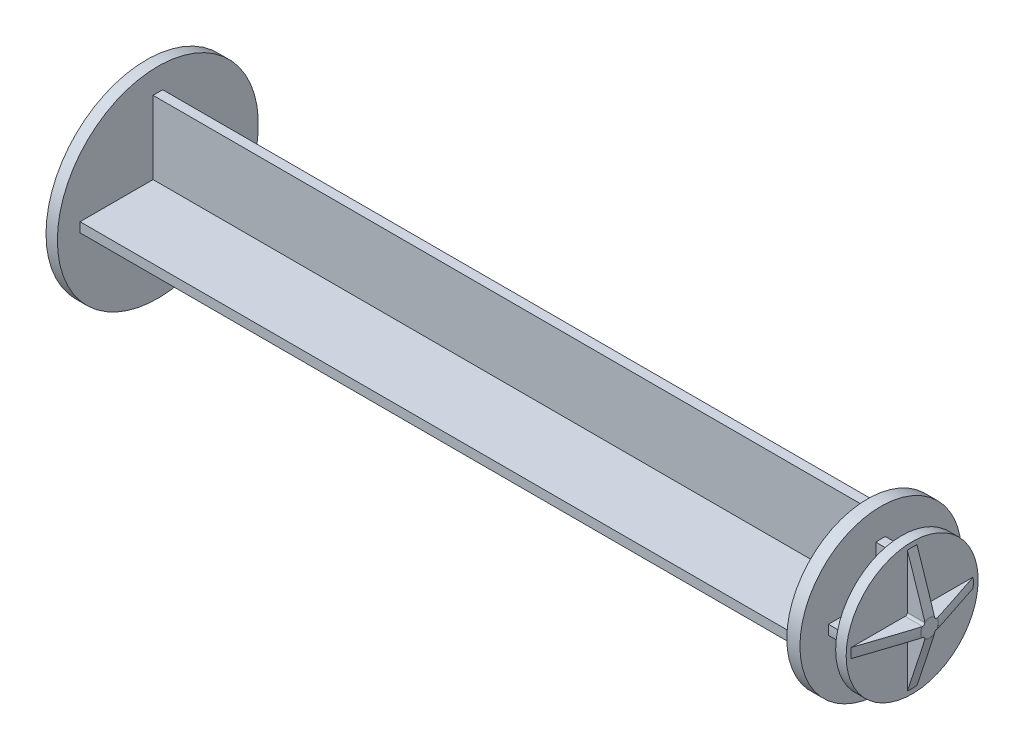
SolidWorks part; units mm, degrees
ref_plane "Front Plane" through (0, 0, 0) normal (0, 0, 1) x (1, 0, 0)
ref_plane "Top Plane" through (0, 0, 0) normal (0, 1, 0) x (1, 0, 0)
ref_plane "Right Plane" through (0, 0, 0) normal (1, 0, 0) x (0, 0, -1)
sketch "Sketch1" plane through (0, 0, 0) normal (0, 0, 1) x (1, 0, 0)
  line L0 (-3.3056, 0) -> (125.6458, 0) construction
  line L1 (16.4016, 0) -> (-16.4016, 0) construction
  line L2 (0, 0) -> (0, 14.605)
  line L3 (0, 14.605) -> (1.651, 14.605)
  line L4 (1.651, 14.605) -> (1.651, 11.7348)
  line L5 (1.651, 11.7348) -> (106.68, 11.7348)
  line L7 (111.252, 8.89) -> (113.7757, 1.3189)
  line L8 (113.792, 1.2185) -> (113.792, 0)
  line L9 (113.792, 0) -> (0, 0)
  line L10 (0, -16.3918) -> (0, 16.3918) construction
  line L12 (106.68, 11.7348) -> (106.68, 9.5885)
  line L13 (106.68, 9.5885) -> (111.252, 9.5885)
  line L14 (111.252, 9.5885) -> (111.252, 8.89)
  arc A0 (113.7757, 1.3189) -> (113.792, 1.2185) centre (113.4745, 1.2185) cw
  point P15 (113.792, 1.27)
  dimension "D10" = 0.3175
  dimension "D1" = 1.651
  dimension "D2" = 29.21
  dimension "D3" = 23.4696
  dimension "D4" = 106.68
  dimension "D5" = 17.78
  dimension "D6" = 19.177
  dimension "D7" = 2.54
  dimension "D8" = 111.252
  dimension "D9" = 2.54
revolve "Revolve: Main Body" add sketch "Sketch1" angle 360 about L0
sketch "Sketch2" plane through (1.651, 0, 0) normal (1, 0, 0) x (0, 0, -1)
  line L0 (0, 7.732) -> (0, -7.732) construction
  line L1 (-0.6985, 11.303) -> (0.6985, 11.303)
  line L2 (-0.6985, 11.303) -> (-0.6985, 0.6985)
  line L3 (-0.6985, -11.303) -> (0.6985, -11.303)
  line L4 (0.6985, 11.303) -> (0.6985, 0.6985)
  line L5 (-11.303, 0.6985) -> (-0.6985, 0.6985)
  line L6 (-11.303, 0.6985) -> (-11.303, -0.6985)
  line L7 (-11.303, -0.6985) -> (-0.6985, -0.6985)
  line L8 (11.303, 0.6985) -> (11.303, -0.6985)
  line L9 (-7.732, 0) -> (7.732, 0) construction
  line L10 (16.4016, 0) -> (-16.4016, 0) construction
  line L11 (0, 18.1835) -> (0, -18.1835) construction
  line L12 (0.6985, 0.6985) -> (11.303, 0.6985)
  line L13 (-0.6985, -0.6985) -> (-0.6985, -11.303)
  line L14 (0.6985, -0.6985) -> (11.303, -0.6985)
  line L15 (0.6985, -0.6985) -> (0.6985, -11.303)
  dimension "D1" = 1.397
  dimension "D2" = 1.397
  dimension "D3" = 22.606
  dimension "D4" = 22.606
extrude "Cut-Extrude: Pusher Side Cross" cut sketch "Sketch2" along normal offset from surface (103.124 mm away) 1.905 flip side to cut up to face at (106.68, 0, 11.7348)
sketch "Sketch3" plane through (106.68, 0, 0) normal (1, 0, 0) x (0, 0, -1)
  line L0 (-11.303, 0.6985) -> (-0.6985, 0.6985) construction
  line L1 (-11.303, -0.6985) -> (-0.6985, -0.6985) construction
  line L2 (-0.6985, -0.6985) -> (-0.6985, -11.303) construction
  line L3 (0.6985, -0.6985) -> (0.6985, -11.303) construction
  line L4 (0.6985, -0.6985) -> (11.303, -0.6985) construction
  line L5 (0.6985, 0.6985) -> (11.303, 0.6985) construction
  line L6 (0.6985, 11.303) -> (0.6985, 0.6985) construction
  line L7 (-0.6985, 11.303) -> (-0.6985, 0.6985) construction
  line L8 (-11.714, 0.6985) -> (-0.6985, 0.6985)
  line L9 (-11.714, -0.6985) -> (-0.6985, -0.6985)
  line L10 (-0.6985, -0.6985) -> (-0.6985, -11.714)
  line L11 (0.6985, -0.6985) -> (0.6985, -11.714)
  line L12 (0.6985, -0.6985) -> (11.714, -0.6985)
  line L13 (0.6985, 0.6985) -> (11.714, 0.6985)
  line L14 (0.6985, 11.714) -> (0.6985, 0.6985)
  line L15 (-0.6985, 11.714) -> (-0.6985, 0.6985)
  line L20 (-7.8512, 0) -> (7.8512, 0) construction
  line L21 (0, 7.8512) -> (0, -7.8512) construction
  line L22 (0, 18.1835) -> (0, -18.1835) construction
  line L23 (16.4016, 0) -> (-16.4016, 0) construction
  arc A1 (-0.6985, 11.714) -> (-11.714, 0.6985) centre (0, 0) ccw
  arc A2 (-11.714, -0.6985) -> (-0.6985, -11.714) centre (0, 0) ccw
  arc A3 (0.6985, -11.714) -> (11.714, -0.6985) centre (0, 0) ccw
  arc A4 (11.714, 0.6985) -> (0.6985, 11.714) centre (0, 0) ccw
  circle A5 centre (0, 0) radius 11.7348 construction
  arc A6 (-7.5879, 0.6985) -> (-7.5879, -0.6985) centre (0, 0) ccw
  arc A7 (7.5879, -0.6985) -> (7.5879, 0.6985) centre (0, 0) ccw
  arc A8 (0.6985, 7.5879) -> (-0.6985, 7.5879) centre (0, 0) ccw
  arc A9 (-0.6985, -7.5879) -> (0.6985, -7.5879) centre (0, 0) ccw
  circle M18 centre (0, 0) radius 11.7348
  circle M19 centre (0, 0) radius 9.5885
  dimension "D1" = 15.24
extrude "Cut-Extrude: Cross 2" cut sketch "Sketch3" along normal blind 3.048 contours L15 L8 M18 M19 | L14 L13 M18 M19 | L12 L11 M19 M18 | L10 L9 M19 M18 | L15 L8 M19 | L14 L13 M19 | L12 L11 M19 | L10 L9 M19 | A9 L10 L11 M19 | A8 L14 L15 M19 | L15 L14 M18 M19 | L11 L10 M19 M18 | L13 L12 M19 M18 | A7 L12 L13 M19 | A6 L8 L9 M19 | L9 L8 M18 M19
sketch "Sketch8" plane through (111.252, 0, 0) normal (1, 0, 0) x (0, 0, -1)
  line L0 (0, 17.301) -> (0, -16.5309) construction
  line L1 (-17.0864, 0) -> (21.0807, 0) construction
  line L2 (0.6985, 0.6985) -> (7.5879, 0.6985) construction
  line L3 (-0.6985, -14.5883) -> (0.6985, -14.5883)
  line L4 (-0.6985, -14.5883) -> (-0.6985, -1.016)
  line L5 (-0.6985, 14.5883) -> (0.6985, 14.5883)
  line L6 (0.6985, -14.5883) -> (0.6985, -1.016)
  line L7 (-0.6985, -14.5883) -> (0.6985, 14.5883) construction
  line L8 (-0.6985, 14.5883) -> (0.6985, -14.5883) construction
  line L9 (14.5883, -0.6985) -> (1.016, -0.6985)
  line L10 (14.5883, -0.6985) -> (14.5883, 0.6985)
  line L11 (14.5883, 0.6985) -> (1.016, 0.6985)
  line L12 (-14.5883, -0.6985) -> (-14.5883, 0.6985)
  line L13 (14.5883, -0.6985) -> (-14.5883, 0.6985) construction
  line L14 (14.5883, 0.6985) -> (-14.5883, -0.6985) construction
  line L15 (0.6985, 7.5879) -> (0.6985, 0.6985) construction
  line L16 (-1.016, 0.6985) -> (-14.5883, 0.6985)
  line L17 (-0.6985, 1.016) -> (-0.6985, 14.5883)
  line L19 (0.6985, 1.016) -> (0.6985, 14.5883)
  line L23 (-1.016, -0.6985) -> (-14.5883, -0.6985)
  circle A0 centre (0, 0) radius 8.89 construction
  circle A1 centre (0, 0) radius 14.605 construction
  arc A2 (-1.016, 0.6985) -> (-0.6985, 1.016) centre (-1.016, 1.016) ccw
  arc A3 (1.016, 0.6985) -> (0.6985, 1.016) centre (1.016, 1.016) cw
  arc A4 (-0.6985, -1.016) -> (-1.016, -0.6985) centre (-1.016, -1.016) ccw
  arc A5 (0.6985, -1.016) -> (1.016, -0.6985) centre (1.016, -1.016) cw
  point P29 (-0.6985, 0.6985)
  point P34 (0.6985, 0.6985)
  dimension "D1" = 0.3175
extrude "Cut-Extrude1" cut sketch "Sketch8" along normal through all flip side to cut
